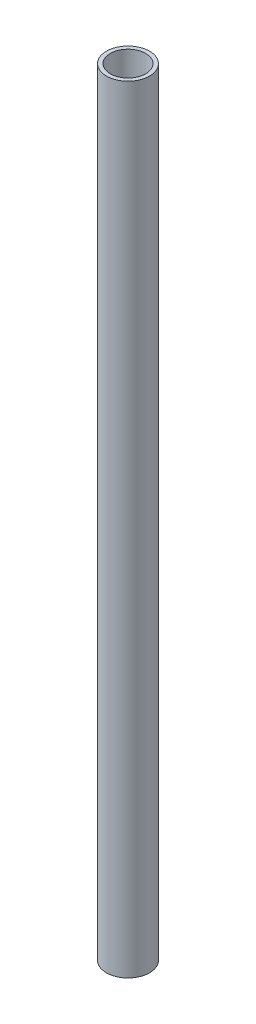
SolidWorks part; units mm, degrees
ref_plane "Front Plane" through (0, 0, 0) normal (0, 0, 1) x (1, 0, 0)
ref_plane "Top Plane" through (0, 0, 0) normal (0, 1, 0) x (1, 0, 0)
ref_plane "Right Plane" through (0, 0, 0) normal (1, 0, 0) x (0, 0, -1)
sketch "Sketch1" plane through (0, 0, 0) normal (0, 1, 0) x (1, 0, 0)
  circle A0 centre (0, 0) radius 12.7
  circle A1 centre (0, 0) radius 10.414
  dimension "D1" = 25.4
  dimension "D2" = 20.828
extrude "Boss-Extrude1" add sketch "Sketch1" along normal blind 457.2
